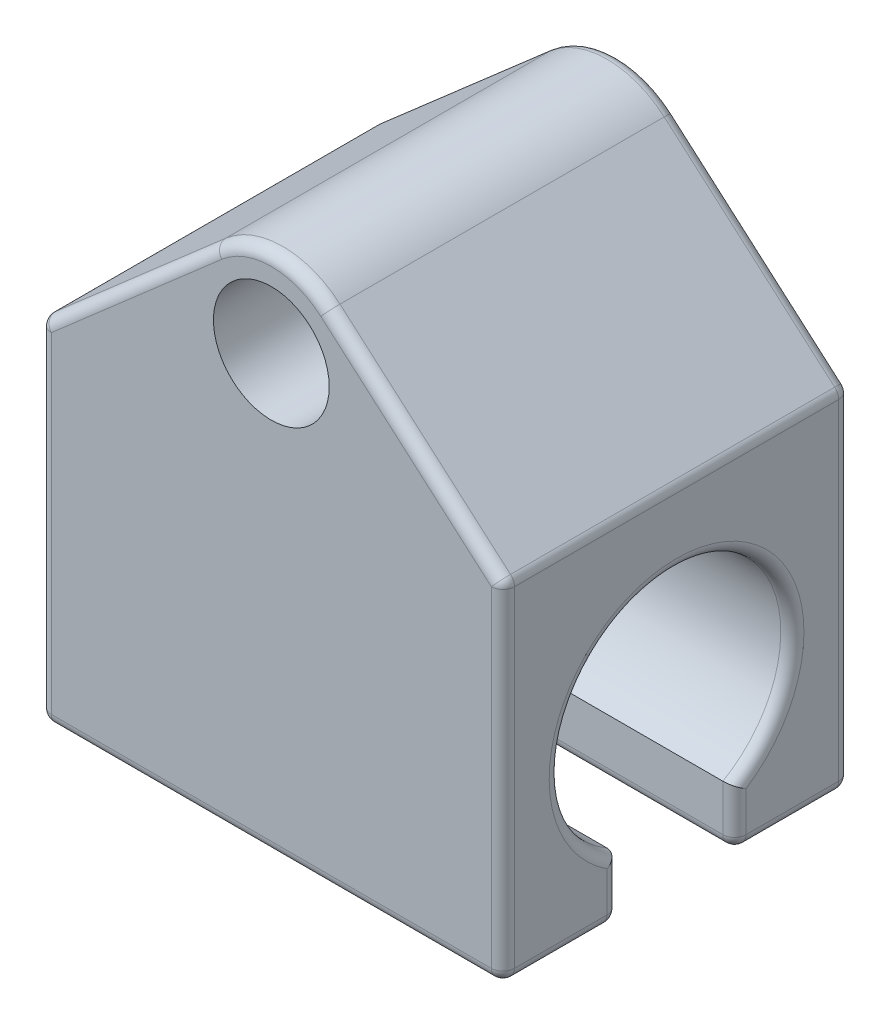
SolidWorks part; units mm, degrees
material "3.1645 (EN-AW 2030)"
ref_plane "前视基准面" through (0, 0, 0) normal (0, 0, 1) x (1, 0, 0)
ref_plane "上视基准面" through (0, 0, 0) normal (0, 1, 0) x (1, 0, 0)
ref_plane "右视基准面" through (0, 0, 0) normal (1, 0, 0) x (0, 0, -1)
sketch "Sketch1" plane through (0, 0, 0) normal (1, 0, 0) x (0, 0, -1)
  line L0 (0, 14.799) -> (0, -14.799) construction
  line L1 (5, -8.6603) -> (5, -13.6603)
  line L2 (-5, -8.6603) -> (-5, -13.6603)
  line L3 (-5, -13.6603) -> (-15, -13.6603)
  line L4 (-15, -13.6603) -> (-15, 16.3397)
  line L5 (-15, 16.3397) -> (15, 16.3397)
  line L6 (5, -13.6603) -> (15, -13.6603)
  line L7 (15, -13.6603) -> (15, 16.3397)
  arc A0 (5, -8.6603) -> (-5, -8.6603) centre (0, 0) ccw
  point P14 (0, 16.3397)
  dimension "D1" = 10
  dimension "D2" = 5
  dimension "D3" = 10
  dimension "D4" = 30
  dimension "D5" = 10
extrude "Boss-Extrude1" add sketch "Sketch1" along normal mid plane 40
sketch "Sketch3" plane through (0, 0, 15) normal (0, 0, 1) x (1, 0, 0)
  line L0 (-20, 16.3397) -> (20, 16.3397)
  line L4 (-20, 16.3397) -> (-4.9315, 29.4904)
  line L5 (20, 16.3397) -> (4.9315, 29.4904)
  circle A0 centre (0, 23.8397) radius 5
  arc A1 (4.9315, 29.4904) -> (-4.9315, 29.4904) centre (0, 23.8397) ccw
  point P4 (0, 16.3397)
  point P5 (0, 0)
  point P8 (0, 0)
  dimension "D1" = 10
  dimension "D2" = 15
extrude "Boss-Extrude2" add sketch "Sketch3" against normal up to surface (30 mm away) up to face at (0, 1.3397, -15)
fillet "Fillet1" radius 1 26 edges at (0, -13.6603, -15) (12.4658, 22.9151, -15) (12.4658, 22.9151, 15) (0, 31.3397, -15) (0, 31.3397, 15) (-12.4658, 22.9151, -15) (-12.4658, 22.9151, 15) (20, -11.1603, 5) (20, -13.6603, 10) (20, 16.3397, 0) (20, 1.3397, -15) (20, -13.6603, -10) (20, -11.1603, -5) (20, 10, 0) (20, 1.3397, 15) (0, -13.6603, 15) (-20, -11.1603, -5) (-20, -13.6603, -10) (-20, 1.3397, -15) (-20, 16.3397, 0) (-20, 1.3397, 15) (-20, -13.6603, 10) (-20, -11.1603, 5) (-20, 10, 0) (0, -13.6603, 5) (0, -13.6603, -5)
